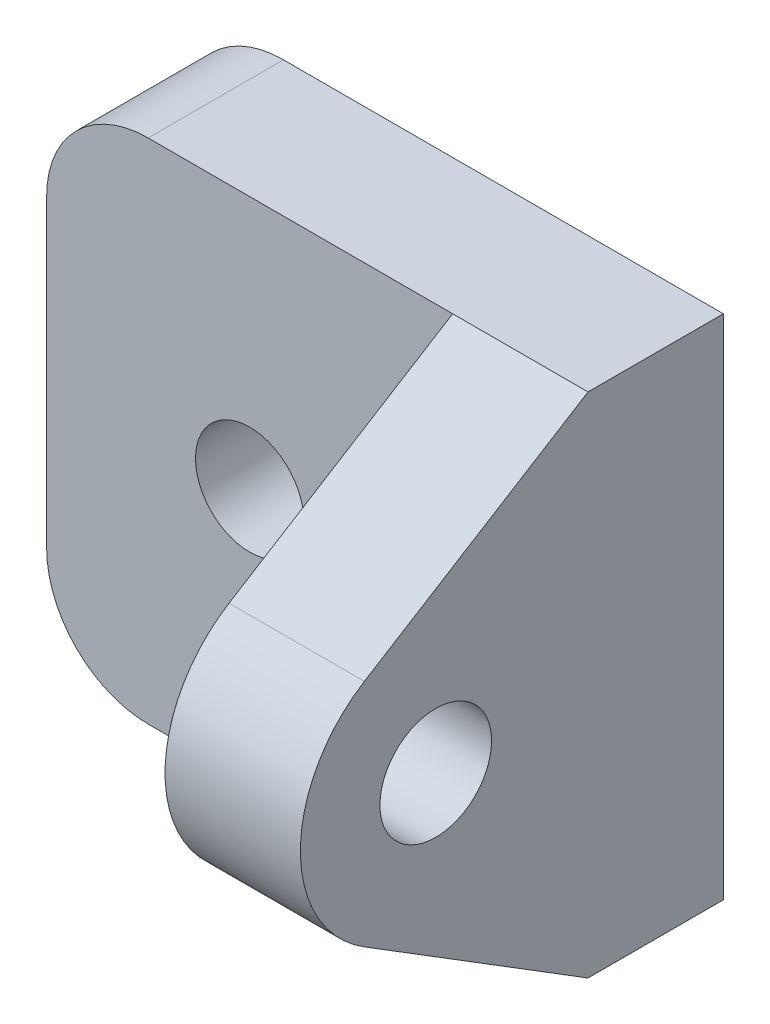
SolidWorks part; units mm, degrees
ref_plane "Front Plane" through (0, 0, 0) normal (0, 0, 1) x (1, 0, 0)
ref_plane "Top Plane" through (0, 0, 0) normal (0, 1, 0) x (1, 0, 0)
ref_plane "Right Plane" through (0, 0, 0) normal (1, 0, 0) x (0, 0, -1)
sketch "Sketch1" plane through (0, 0, 0) normal (0, 0, 1) x (1, 0, 0)
  line L1 (14, -7.5) -> (-14, -7.5)
  line L2 (14, -7.5) -> (14, 7.5)
  line L3 (14, 7.5) -> (-14, 7.5)
  line L4 (-14, -7.5) -> (-14, 7.5)
  line L5 (14, -7.5) -> (-14, 7.5) construction
  line L6 (14, 7.5) -> (-14, -7.5) construction
  point P0 (0, 0)
  dimension "D1" = 15
  dimension "D2" = 28
extrude "Boss-Extrude1" add sketch "Sketch1" along normal blind 4
sketch "Sketch3" plane through (-14, 0, 0) normal (-1, 0, 0) x (0, 0, 1)
  line L0 (4, 7.5) -> (4, -7.5)
  line L1 (4, -7.5) -> (10.6088, -3.3999)
  line L2 (4, 7.5) -> (10.6094, 3.3977)
  circle A0 centre (8.5, -0.0009) radius 4
  circle A1 centre (8.5, -0.0009) radius 1.65
  line M4 (4, -7.5) -> (4, 7.5)
  dimension "D1" = 8
  dimension "D3" = 3.3
  dimension "D2" = 4.5
extrude "Boss-Extrude2" add sketch "Sketch3" against normal blind 4 contours A0 L2 L1 M4 | A0 A1
sketch "Sketch5" plane through (0, 0, 0) normal (0, 0, -1) x (-1, 0, 0)
  line L1 (14, -7.5) -> (26, -7.5)
  line L2 (14, -7.5) -> (14, 7.5)
  line L3 (14, 7.5) -> (26, 7.5)
  line L4 (26, -7.5) -> (26, 7.5)
  circle A0 centre (20, 0) radius 1.6
  dimension "D2" = 3.2
  dimension "D1" = 12
  dimension "D3" = 6
extrude "Boss-Extrude3" add sketch "Sketch5" against normal up to surface (4 mm away) up to face at (2, 0, 4)
ref_plane "Plane3" through (0, 0, 0) normal (1, 0, 0) x (0, 0, -1)
mirror "Mirror1" about plane through (0, 0, 0) normal (1, 0, 0) of "Boss-Extrude3", "Boss-Extrude2"
fillet "Fillet1" radius 3 4 edges at (-26, 7.5, 2) (26, 7.5, 2) (26, -7.5, 2) (-26, -7.5, 2)
sketch "Sketch6" plane through (0, -7.5, 0) normal (0, -1, 0) x (1, 0, 0)
  line L0 (-23, 0) -> (23, 0) construction
  line L1 (0, 0) -> (37.2803, 0)
  line L3 (0, 22.5019) -> (37.2803, 22.5019)
  line L4 (37.2803, 0) -> (37.2803, 22.5019)
  line L5 (0, 22.5019) -> (-10, 22.5019)
  line L6 (-10, 22.5019) -> (-10, 0)
  line L7 (-10, 0) -> (0, 0)
extrude "Cut-Extrude1" cut sketch "Sketch6" against normal blind 15
